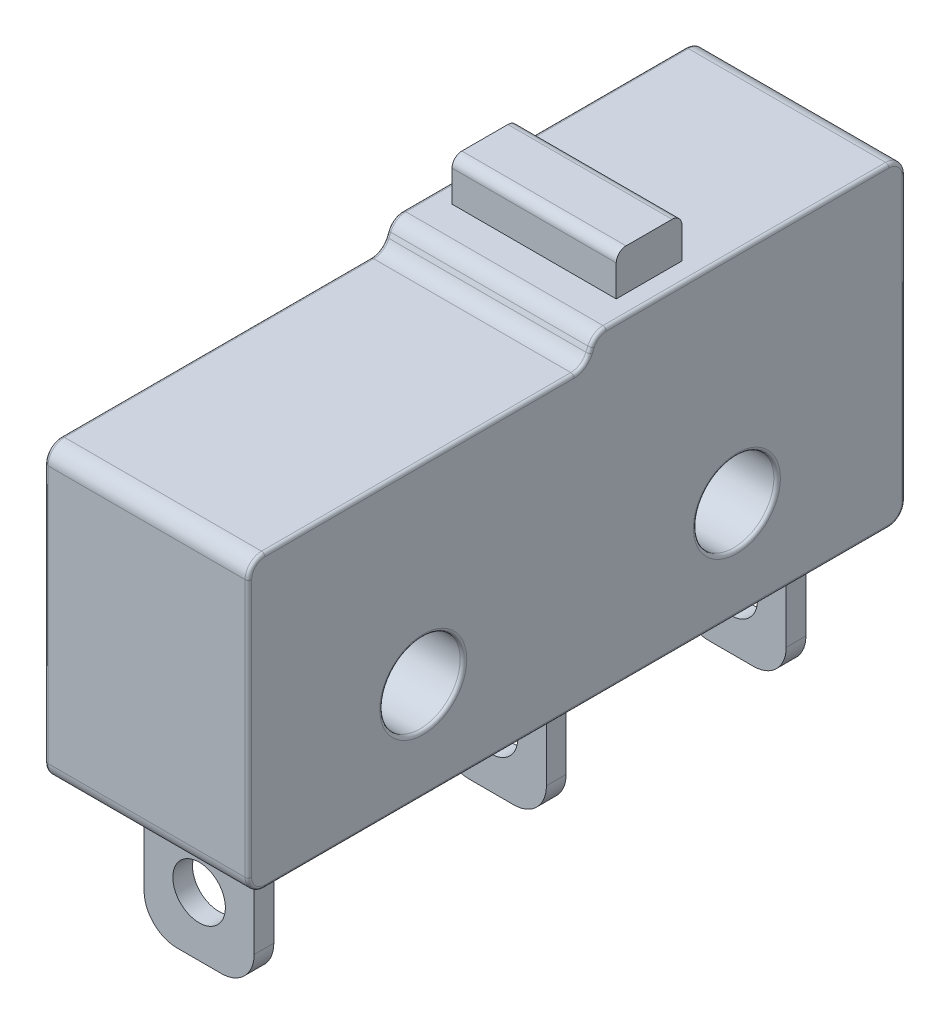
SolidWorks part; units mm, degrees
ref_plane "Front" through (0, 0, 0) normal (0, 0, 1) x (1, 0, 0)
ref_plane "Top" through (0, 0, 0) normal (0, 1, 0) x (1, 0, 0)
ref_plane "Right" through (0, 0, 0) normal (1, 0, 0) x (0, 0, -1)
sketch "Sketch1" plane through (0, 0, 0) normal (1, 0, 0) x (0, 0, -1)
  line L0 (10.563, 9.6) -> (10.25, 8.85)
  line L1 (0, 0) -> (20, 0)
  line L2 (0, 0) -> (0, 8.85)
  line L3 (10.563, 9.6) -> (20, 9.6)
  line L4 (20, 0) -> (20, 9.6)
  line L5 (10.25, 8.85) -> (0, 8.85)
  dimension "D1" = 20
  dimension "D2" = 9.6
  dimension "D3" = 0.75
  dimension "D4" = 9.75
extrude "Boss-Extrude1" add sketch "Sketch1" along normal mid plane 6.2
sketch "Sketch2" plane through (3.1, 0, 0) normal (1, 0, 0) x (0, 0, -1)
  line L1 (0, 8.85) -> (0, 0) construction
  line L2 (0, 0) -> (20, 0) construction
  line L5 (20, 0) -> (20, 9.6) construction
  circle A0 centre (5.325, 2.975) radius 1.225
  circle A1 centre (14.875, 2.975) radius 1.225
  dimension "D1" = 12
  dimension "D2" = 2.45
  dimension "D4" = 4.1
  dimension "D3" = 1.75
  dimension "D5" = 3.9
extrude "Cut-Extrude4" cut sketch "Sketch2" against normal through all
fillet "Fillet1" radius 0.5 6 edges at (0, 0, -20) (0, 9.6, -20) (0, 9.6, -10.563) (0, 8.85, -10.25) (0, 0, 0) (0, 8.85, 0)
fillet "Fillet2" radius 0.1 28 edges at (-3.1, 9.4536, -19.8536) (-3.1, 9.6, -15.1981) (-3.1, 9.5161, -10.6189) (-3.1, 9.225, -10.4065) (-3.1, 8.9339, -10.1941) (-3.1, 8.85, -5.2084) (-3.1, 8.7036, -0.1464) (-3.1, 4.425, 0) (-3.1, 0.1464, -0.1464) (-3.1, 0, -10) (-3.1, 0.1464, -19.8536) (-3.1, 4.8, -20) (-3.1, 2.975, -6.55) (-3.1, 2.975, -16.1) (3.1, 0.1464, -0.1464) (3.1, 4.425, 0) (3.1, 8.7036, -0.1464) (3.1, 8.85, -5.2084) (3.1, 8.9339, -10.1941) (3.1, 9.225, -10.4065) (3.1, 9.5161, -10.6189) (3.1, 9.6, -15.1981) (3.1, 9.4536, -19.8536) (3.1, 4.8, -20) (3.1, 0.1464, -19.8536) (3.1, 0, -10) (3.1, 2.975, -6.55) (3.1, 2.975, -16.1)
sketch "Sketch3" plane through (0, 0, 0) normal (0, -1, 0) x (1, 0, 0)
  line L0 (0, 0) -> (0, -21.0436) construction
  line L1 (-1.675, -1.6) -> (1.675, -1.6)
  line L2 (-1.675, -1.6) -> (-1.675, -2.2)
  line L3 (-1.675, -2.2) -> (1.675, -2.2)
  line L4 (1.675, -1.6) -> (1.675, -2.2)
  line L5 (-1.675, -10.5) -> (1.675, -10.5)
  line L6 (-1.675, -10.5) -> (-1.675, -11.1)
  line L7 (-1.675, -11.1) -> (1.675, -11.1)
  line L8 (1.675, -10.5) -> (1.675, -11.1)
  line L9 (-1.675, -17.8) -> (1.675, -17.8)
  line L10 (-1.675, -17.8) -> (-1.675, -18.4)
  line L11 (-1.675, -18.4) -> (1.675, -18.4)
  line L12 (1.675, -17.8) -> (1.675, -18.4)
  dimension "D1" = 0.6
  dimension "D2" = 3.35
  dimension "D3" = 1.6
  dimension "D4" = 8.3
  dimension "D5" = 6.7
extrude "Boss-Extrude2" add sketch "Sketch3" along normal blind 4
sketch "Sketch4" plane through (0, 0, -18.4) normal (0, 0, -1) x (-1, 0, 0)
  line L0 (0, 0) -> (0, -4.8406) construction
  line L1 (1.675, -4) -> (-1.675, -4) construction
  circle A0 centre (0, -2.2) radius 0.8
  dimension "D1" = 1.6
  dimension "D2" = 1
extrude "Cut-Extrude5" cut sketch "Sketch4" against normal through all
fillet "Fillet3" radius 1 6 edges at (-1.675, -4, -18.1) (-1.675, -4, -10.8) (-1.675, -4, -1.9) (1.675, -4, -1.9) (1.675, -4, -10.8) (1.675, -4, -18.1)
sketch "Sketch5" plane through (0, 0, 0) normal (1, 0, 0) x (0, 0, -1)
  line L0 (11.8, 9.6) -> (11.8, 10.55)
  line L1 (10.8961, 9.6) -> (19.5, 9.6) construction
  line L2 (12.1, 10.85) -> (13.5, 10.85)
  line L3 (13.8, 10.55) -> (13.8, 9.6)
  line L4 (13.8, 9.6) -> (11.8, 9.6)
  line L5 (20, 9.1) -> (20, 0.5) construction
  arc A0 (13.5, 10.85) -> (13.8, 10.55) centre (13.5, 10.55) cw
  arc A1 (11.8, 10.55) -> (12.1, 10.85) centre (12.1, 10.55) cw
  dimension "D1" = 0.3
  dimension "D2" = 1.25
  dimension "D3" = 2
  dimension "D4" = 6.2
extrude "Boss-Extrude3" add sketch "Sketch5" along normal mid plane 5
